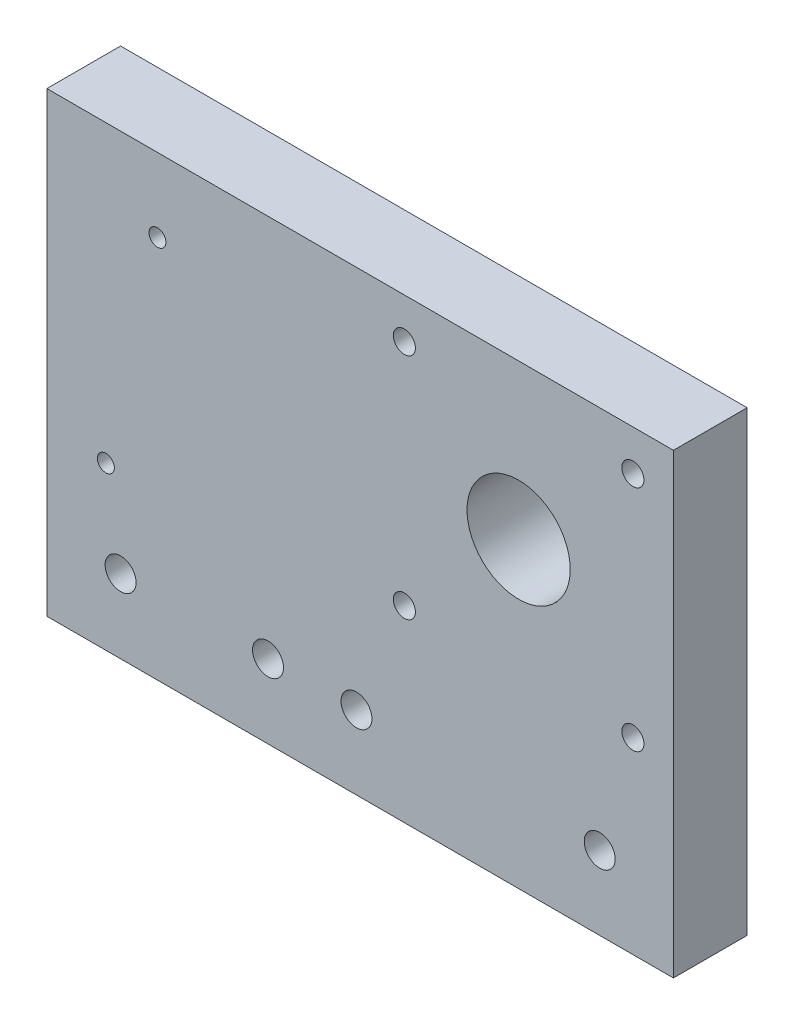
SolidWorks part; units mm, degrees
ref_plane "Front Plane" through (0, 0, 0) normal (0, 0, 1) x (1, 0, 0)
ref_plane "Top Plane" through (0, 0, 0) normal (0, 1, 0) x (1, 0, 0)
ref_plane "Right Plane" through (0, 0, 0) normal (1, 0, 0) x (0, 0, -1)
sketch "Sketch1" plane through (0, 0, 0) normal (0, 0, 1) x (1, 0, 0)
  line L5 (0, 62) -> (85, 62)
  line L6 (0, 62) -> (0, 0)
  line L7 (0, 0) -> (85, 0)
  line L8 (85, 62) -> (85, 0)
  circle A0 centre (8, 22) radius 1.15
  circle A1 centre (15, 52) radius 1.15
  circle A2 centre (10, 10) radius 2.1
  circle A3 centre (30, 10) radius 2.1
  circle A4 centre (42, 10) radius 2.1
  circle A5 centre (75, 10) radius 2.1
  circle A6 centre (64, 41) radius 7
  circle A7 centre (48.5, 56.5) radius 1.5
  circle A8 centre (79.5, 56.5) radius 1.5
  circle A9 centre (79.5, 25.5) radius 1.5
  circle A10 centre (48.5, 25.5) radius 1.5
  dimension "D3" = 8
  dimension "D7" = 2.3
  dimension "D8" = 85
  dimension "D4" = 15
  dimension "D5" = 10
  dimension "D6" = 22
  dimension "D9" = 4.2
  dimension "D16" = 3
  dimension "D21" = 14
  dimension "D10" = 10
  dimension "D11" = 10
  dimension "D12" = 10
  dimension "D13" = 12
  dimension "D14" = 30
  dimension "D15" = 62
  dimension "D17" = 31
  dimension "D18" = 31
  dimension "D19" = 21
  dimension "D20" = 21
  dimension "D22" = 15.5
  dimension "D23" = 15.5
extrude "Boss-Extrude1" add sketch "Sketch1" along normal blind 10
